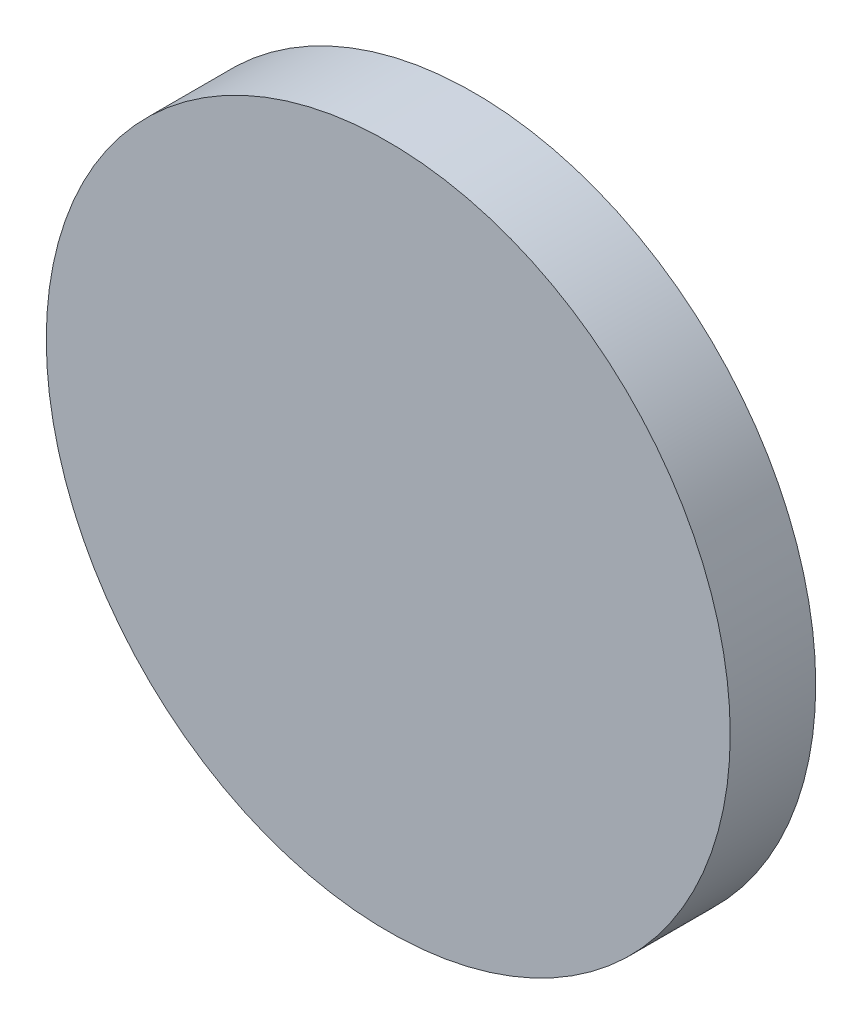
SolidWorks part; units mm, degrees
material "Acrylic (Medium-high impact)"
ref_plane "Front Plane" through (0, 0, 0) normal (0, 0, 1) x (1, 0, 0)
ref_plane "Top Plane" through (0, 0, 0) normal (0, 1, 0) x (1, 0, 0)
ref_plane "Right Plane" through (0, 0, 0) normal (1, 0, 0) x (0, 0, -1)
sketch "Sketch1" plane through (0, 0, 0) normal (0, 0, 1) x (1, 0, 0)
  circle A0 centre (0, 0) radius 25.4
  dimension "D1" = 50.8
extrude "Boss-Extrude1" add sketch "Sketch1" along normal blind 6.35
